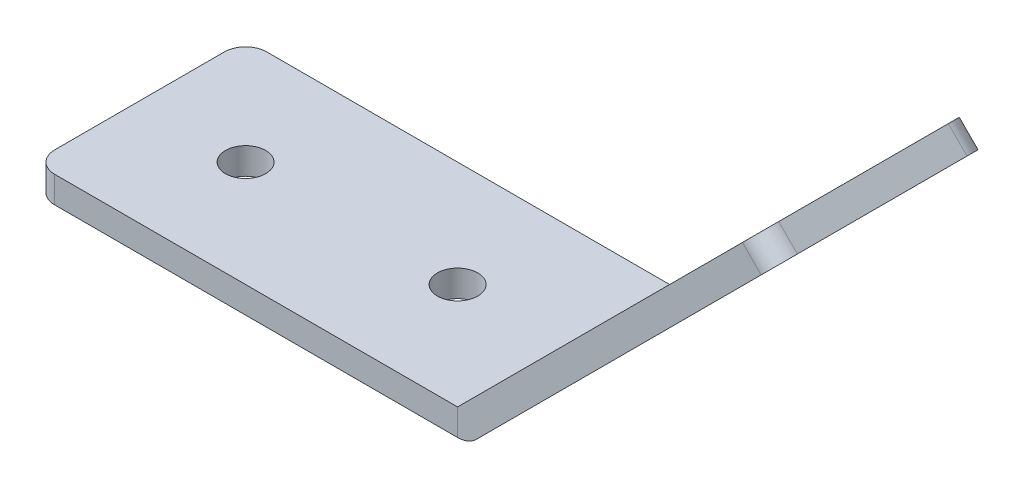
SolidWorks part; units mm, degrees
ref_plane "Front Plane" through (0, 0, 0) normal (0, 0, 1) x (1, 0, 0)
ref_plane "Top Plane" through (0, 0, 0) normal (0, 1, 0) x (1, 0, 0)
ref_plane "Right Plane" through (0, 0, 0) normal (1, 0, 0) x (0, 0, -1)
sketch "Sketch1" plane through (0, 0, 0) normal (0, 1, 0) x (1, 0, 0)
  line L1 (0, 0) -> (50.8, 0)
  line L2 (0, 0) -> (0, -25.4)
  line L3 (0, -25.4) -> (50.8, -25.4)
  line L4 (50.8, 0) -> (50.8, -25.4)
  dimension "D1" = 50.8
  dimension "D2" = 25.4
extrude "Boss-Extrude1" add sketch "Sketch1" along normal blind 3.175
sketch "Sketch2" plane through (0, 0, 25.4) normal (0, 0, 1) x (1, 0, 0)
  line L0 (50.8, 3.175) -> (86.721, 39.096)
  line L1 (0, 3.175) -> (50.8, 3.175) construction
  line L3 (53.0451, 0.9299) -> (88.9661, 36.851)
  line L4 (88.9661, 36.851) -> (86.721, 39.096)
  line L5 (0, 0) -> (50.8, 0) construction
  line L6 (50.8, 3.175) -> (50.8, 0)
  arc A0 (50.8, 0) -> (53.0451, 0.9299) centre (50.8, 3.175) ccw
  dimension "D1" = 50.8
  dimension "D2" = 135
  dimension "D3" = 3.175
  dimension "D4" = 135
extrude "Boss-Extrude2" add sketch "Sketch2" against normal up to surface (25.4 mm away) separate body up to face at (25.4, 1.5875, 0)
sketch "Sketch4" plane through (0, 3.175, 0) normal (0, 1, 0) x (1, 0, 0)
  line L0 (0, 0) -> (0, -25.4) construction
  line L1 (0, -12.7) -> (50.8, -12.7) construction
  line L2 (50.8, 0) -> (50.8, -25.4) construction
  circle A0 centre (38.1, -12.7) radius 2.413
  circle A1 centre (12.7, -12.7) radius 2.413
  point P10 (38.1, -12.7)
  point P11 (12.7, -12.7)
  dimension "D1" = 4.826
  dimension "D2" = 4.826
  dimension "D3" = 25.4
  dimension "D4" = 12.7
extrude "Cut-Extrude1" cut sketch "Sketch4" against normal up to surface (3.175 mm away) up to face at (25.4, 0, 12.7)
sketch "Sketch5" plane through (23.8125, -23.8125, 0) normal (-0.7071, 0.7071, 0) x (0, 0, 1)
  line L0 (12.7, 38.1661) -> (12.7, 88.9661) construction
  line L1 (25.4, 38.1661) -> (0, 38.1661) construction
  line L2 (0, 88.9661) -> (25.4, 88.9661) construction
  circle A0 centre (12.7, 50.8661) radius 2.413
  circle A1 centre (12.7, 76.2661) radius 2.413
  dimension "D1" = 4.826
  dimension "D2" = 4.826
  dimension "D3" = 25.4
  dimension "D4" = 12.7
extrude "Cut-Extrude2" cut sketch "Sketch5" against normal up to surface (3.175 mm away) up to face at (71.0056, 18.8904, 12.7)
fillet "Fillet1" radius 2.54 2 edges at (87.8436, 37.9735, 25.4) (87.8436, 37.9735, 0)
fillet "Fillet2" radius 2.54 2 edges at (0, 1.5875, 25.4) (0, 1.5875, 0)
